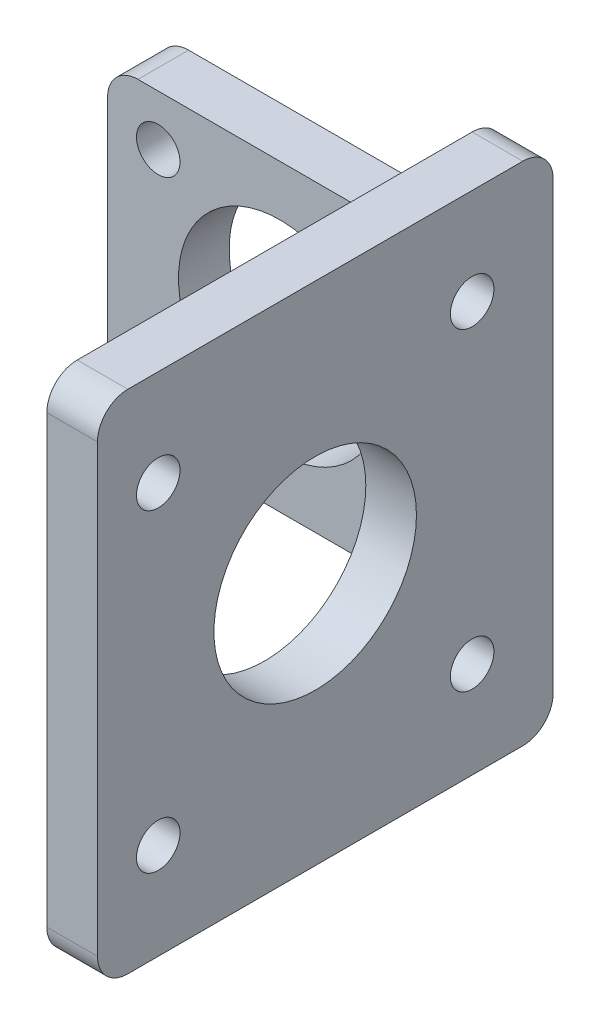
SolidWorks part; units mm, degrees
material "Balsa"
ref_plane "前视基准面" through (0, 0, 0) normal (0, 0, 1) x (1, 0, 0)
ref_plane "上视基准面" through (0, 0, 0) normal (0, 1, 0) x (1, 0, 0)
ref_plane "右视基准面" through (0, 0, 0) normal (1, 0, 0) x (0, 0, -1)
other "Configuration Table"
sketch "Sketch2" plane through (0, 0, 0) normal (0, 0, 1) x (1, 0, 0)
  line L4 (34, -30) -> (34, 0)
  line L5 (0, -30) -> (34, -30)
  line L6 (0, 0) -> (0, -30)
  line L7 (34, 0) -> (0, 0)
  line L8 (0, -15) -> (34, -15) construction
  line L9 (17, 0) -> (17, -30) construction
  circle A0 centre (17, -15) radius 10
  circle A1 centre (29, -5) radius 2.15
  circle A6 centre (5, -5) radius 2.15
  circle A8 centre (5, -25) radius 2.15
  circle A9 centre (29, -25) radius 2.15
  point P22 (17, 0)
  point P23 (0, -15)
  dimension "D1" = 4.3
  dimension "D2" = 24
  dimension "D3" = 20
  dimension "D4" = 20
  dimension "D5" = 34
  dimension "D6" = 30
extrude "Boss-Extrude1" add sketch "Sketch2" along normal blind 5
sketch "Sketch6" plane through (0, 0, 5) normal (0, 0, 1) x (1, 0, 0)
  line L0 (34, -30) -> (34, 0) construction
  line L1 (34, 10) -> (39, 10)
  line L2 (34, 10) -> (34, -40)
  line L3 (34, -40) -> (39, -40)
  line L4 (39, 10) -> (39, -40)
  point P6 (34, -15)
  point P7 (34, -15)
  dimension "D1" = 50
  dimension "D2" = 5
extrude "Boss-Extrude3" add sketch "Sketch6" along normal blind 40
sketch "Sketch7" plane through (39, 0, 0) normal (1, 0, 0) x (0, 0, -1)
  line L4 (-48, 0.913) -> (-5, 0.913)
  line L5 (-48, 0.913) -> (-48, -42.087)
  line L6 (-48, -42.087) -> (-5, -42.087)
  line L10 (-5, 0.913) -> (-5, -42.087)
  line L11 (-26.5, 17.8548) -> (-26.5, -52.6873) construction
  line L12 (-48, -20.587) -> (-5.464, -20.587) construction
  line L13 (-45, -40) -> (-45, 10) construction
  line L14 (-45, -40) -> (-5, -40) construction
  circle A7 centre (-26.5, -20.587) radius 10
  circle A8 centre (-42, -5.087) radius 1.65
  circle A9 centre (-11, -5.087) radius 1.65
  circle A10 centre (-42, -5.087) radius 1.65
  circle A11 centre (-11, -5.087) radius 1.65
  circle A12 centre (-11, -36.087) radius 1.65
  circle A13 centre (-42, -36.087) radius 1.65
  dimension "D1" = 3.3
  dimension "D2" = 3
  dimension "D3" = 18.5
  dimension "D4" = 40
  dimension "D5" = 3
  dimension "D6" = 3.913
  dimension "D7" = 20
  dimension "D8" = 19.413
  dimension "D9" = 40.913
sketch "Sketch10" plane through (34, 0, 0) normal (1, 0, 0) x (0, 0, -1)
  line L4 (0, -30) -> (0, 0)
  line L5 (0, 0) -> (-5, 0)
  line L6 (-5, 0) -> (-5, -30)
  line L7 (-5, -30) -> (0, -30)
  line L8 (0, -30) -> (0, 0)
  line L9 (0, 0) -> (-5, 0)
  line L10 (-5, 0) -> (-5, -30)
  line L11 (-5, -30) -> (0, -30)
  dimension "D1" = 0
extrude "Boss-Extrude4" add sketch "Sketch10" along normal up to surface (5 mm away) up to face at (39, -15, 25)
sketch "Sketch11" plane through (0, 0, 5) normal (0, 0, -1) x (-1, 0, 0)
  line L0 (-34, -40) -> (-34, -30) construction
  line L1 (-34, -30) -> (-39, -30) construction
  line L2 (-39, -30) -> (-39, -40) construction
  line L3 (-39, -40) -> (-34, -40) construction
  line L4 (-39, 10) -> (-39, 0) construction
  line L5 (-39, 0) -> (-34, 0) construction
  line L6 (-34, 0) -> (-34, 10) construction
  line L7 (-34, 10) -> (-39, 10) construction
  line L8 (-34, -40) -> (-34, -30)
  line L9 (-34, -30) -> (-39, -30)
  line L10 (-39, -30) -> (-39, -40)
  line L11 (-39, -40) -> (-34, -40)
  line L12 (-39, 10) -> (-39, 0)
  line L13 (-39, 0) -> (-34, 0)
  line L14 (-34, 0) -> (-34, 10)
  line L15 (-34, 10) -> (-39, 10)
extrude "Boss-Extrude5" add sketch "Sketch11" along normal up to surface (5 mm away) up to face at (19.5, -15, 0)
fillet "Fillet3" radius 3 4 edges at (34, -30, 2.5) (34, 0, 2.5) (0, -30, 2.5) (0, 0, 2.5)
fillet "Fillet4" radius 3 1 edges at (36.5, -40, 0)
fillet "Fillet5" radius 3 3 edges at (36.5, -40, 45) (36.5, 10, 45) (36.5, 10, 0)
sketch "Sketch12" plane through (39, 0, 0) normal (1, 0, 0) x (0, 0, -1)
  line L0 (-45, 6.5) -> (-2, 6.5) construction
  line L1 (-45, 6.5) -> (-45, -36.5) construction
  line L2 (-45, -36.5) -> (-2, -36.5) construction
  line L3 (-2, 6.5) -> (-2, -36.5) construction
  line L4 (-23.5, 6.5) -> (-23.5, -36.5) construction
  line L5 (-45, -15) -> (-2, -15) construction
  line L6 (-42, -40) -> (-3, -40) construction
  line L7 (-45, -37) -> (-45, 7) construction
  circle A0 centre (-23.5, -15) radius 10
  circle A1 centre (-39, 0.5) radius 2.15
  circle A2 centre (-8, 0.5) radius 2.15
  circle A3 centre (-39, 0.5) radius 2.15
  circle A4 centre (-8, 0.5) radius 2.15
  circle A5 centre (-8, -30.5) radius 2.15
  circle A6 centre (-39, -30.5) radius 2.15
  point P22 (-2, -15)
  point P25 (0, 0)
  point P26 (-23.5, -45.3439)
  point P27 (0, 0)
  point P28 (0, 0)
  point P29 (-23.5, -36.5)
  point P30 (-23.5, 6.5)
  dimension "D1" = 4.3
  dimension "D2" = 6
  dimension "D3" = 21.5
  dimension "D4" = 43
  dimension "D5" = 3.5
  dimension "D6" = 9.5
  dimension "D7" = 20
  dimension "D8" = 25
extrude "Cut-Extrude3" cut sketch "Sketch12" against normal up to surface (5 mm away) contours A1 | A0 | A2 | A5 | A6 up to face at (34, -15, 15.8333)
